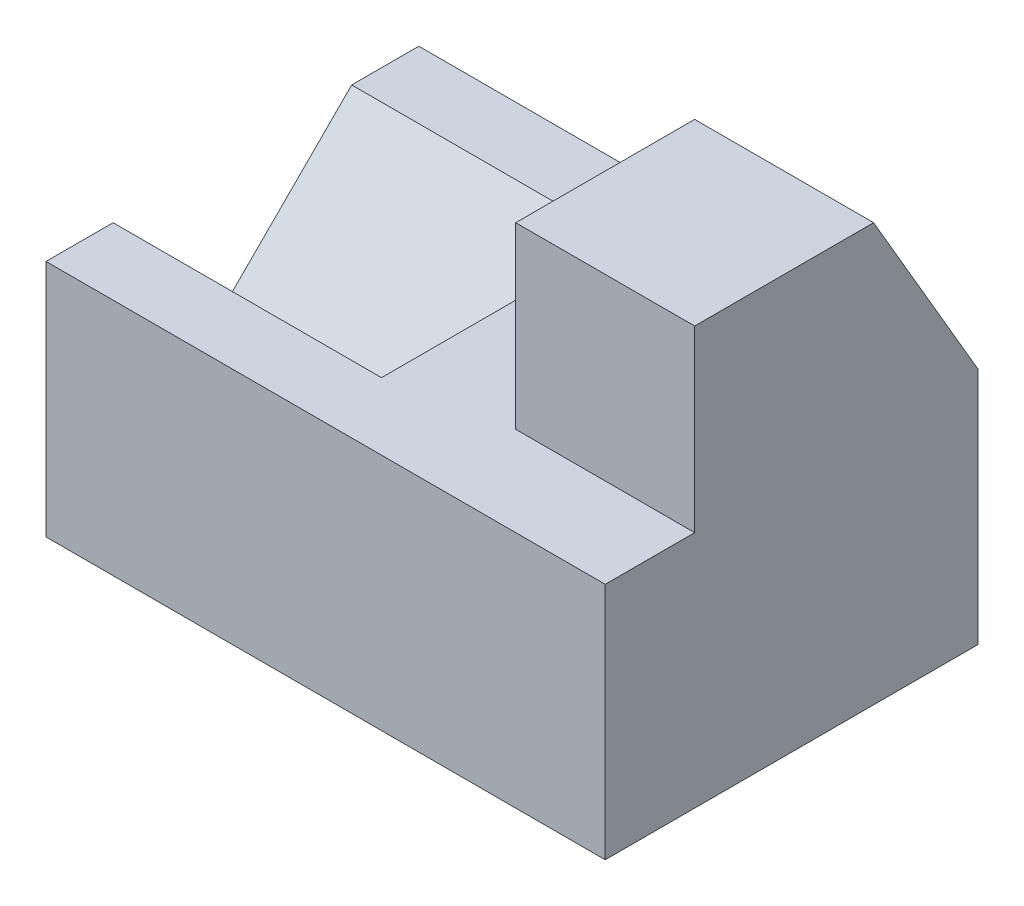
SolidWorks part; units mm, degrees
ref_plane "Front Plane" through (0, 0, 0) normal (0, 0, 1) x (1, 0, 0)
ref_plane "Top Plane" through (0, 0, 0) normal (0, 1, 0) x (1, 0, 0)
ref_plane "Right Plane" through (0, 0, 0) normal (1, 0, 0) x (0, 0, -1)
sketch "Sketch2" plane through (0, 0, 0) normal (0, 1, 0) x (1, 0, 0)
  line L1 (-35.688, 25.8776) -> (39.312, 25.8776)
  line L2 (-35.688, 25.8776) -> (-35.688, -24.1224)
  line L3 (-35.688, -24.1224) -> (39.312, -24.1224)
  line L4 (39.312, 25.8776) -> (39.312, -24.1224)
extrude "Boss-Extrude1" add sketch "Sketch2" along normal blind 32 contours L1 L4 L3 L2
sketch "Sketch4" plane through (-35.688, 0, 0) normal (-1, 0, 0) x (0, 0, 1)
  line L0 (24.1224, 32) -> (24.1224, 0) construction
  line L1 (-25.8776, 0) -> (24.1224, 0)
  line L2 (-25.8776, 0) -> (-25.8776, 16)
  line L3 (-25.8776, 16) -> (24.1224, 16)
  line L4 (24.1224, 0) -> (24.1224, 16)
  line L5 (-16.8776, 32) -> (-0.8776, 16)
  line L6 (-0.8776, 16) -> (15.1224, 32)
  line L7 (15.1224, 32) -> (-16.8776, 32)
extrude "Cut-Extrude1" cut sketch "Sketch4" against normal blind 36 contours L5 L6 L7
sketch "Sketch5" plane through (0, 32, 0) normal (0, 1, 0) x (1, 0, 0)
  line L5 (39.312, -12.1224) -> (15.312, -12.1224)
  line L6 (39.312, -12.1224) -> (39.312, 11.8776)
  line L7 (39.312, 11.8776) -> (15.312, 11.8776)
  line L8 (15.312, -12.1224) -> (15.312, 11.8776)
extrude "Boss-Extrude3" add sketch "Sketch5" along normal blind 24
sketch "Sketch6" plane through (39.312, 0, 0) normal (1, 0, 0) x (0, 0, -1)
  line L0 (11.8776, 56) -> (25.8776, 32)
  line L1 (25.8776, 32) -> (11.8776, 32)
  line L2 (11.8776, 32) -> (11.8776, 56)
extrude "Boss-Extrude4" add sketch "Sketch6" against normal blind 24
